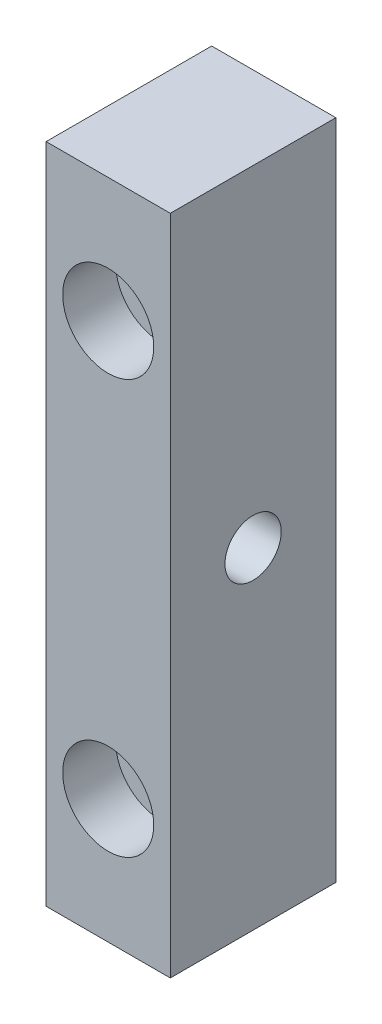
SolidWorks part; units mm, degrees
ref_plane "前视基准面" through (0, 0, 0) normal (0, 0, 1) x (1, 0, 0)
ref_plane "上视基准面" through (0, 0, 0) normal (0, 1, 0) x (1, 0, 0)
ref_plane "右视基准面" through (0, 0, 0) normal (1, 0, 0) x (0, 0, -1)
sketch "草图1" plane through (0, 0, 0) normal (0, 0, 1) x (1, 0, 0)
  line L1 (7.5, -40) -> (-7.5, -40)
  line L2 (7.5, -40) -> (7.5, 40)
  line L3 (7.5, 40) -> (-7.5, 40)
  line L4 (-7.5, -40) -> (-7.5, 40)
  line L5 (7.5, -40) -> (-7.5, 40) construction
  line L6 (7.5, 40) -> (-7.5, -40) construction
  point P0 (0, 0)
  dimension "D1" = 15
  dimension "D2" = 80
extrude "凸台-拉伸1" add sketch "草图1" along normal blind 20
sketch "草图2" plane through (7.5, 0, 0) normal (1, 0, 0) x (0, 0, -1)
  line L0 (-20, 0) -> (-10, 0) construction
  line L1 (-20, -40) -> (-20, 40) construction
  circle A0 centre (-10, 0) radius 4.5781
  dimension "D1" = 10
hole_wizard "M8 螺纹孔1" positions "3D草图1" profile "草图3" tap size "M8" standard "Iso"
sketch3d "3D草图1"
  point P0 (7.5, 0, 10)
sketch "草图3" plane through (7.5, 0, 10) normal (0, 1, 0) x (0, 0, -1)
  line L0 (0, 0) -> (0, 21.7929)
  line L1 (0, 21.7929) -> (3.4, 19.75)
  line L2 (3.4, 19.75) -> (3.4, 0)
  line L5 (3.4, 0) -> (0, 0)
  line L10 (0, 21.7929) -> (-3.4, 19.75) construction
  line L11 (0, -6.35) -> (0, 107.95) construction
  dimension "螺纹孔钻头直径" = 6.8
  dimension "螺纹孔钻头深度" = 19.75
  dimension "导头角度" = 118
sketch "草图4" plane through (0, 0, 20) normal (0, 0, 1) x (1, 0, 0)
  line L0 (0, 25) -> (0, 0) construction
  line L1 (0, 0) -> (-18.5111, 0) construction
  circle A0 centre (0, 25) radius 2.5
  circle A1 centre (0, -25) radius 2.5
  dimension "D1" = 50
hole_wizard "M6 六角凹头螺钉的柱形沉头孔1" positions "3D草图2" profile "草图5" counterbore size "M6" standard "Iso" end condition through all
sketch3d "3D草图2"
  point P0 (0, 25, 20)
  point P3 (0, -25, 20)
sketch "草图5" plane through (0, 25, 20) normal (1, 0, 0) x (0, -1, 0)
  line L0 (0, 0) -> (0, 20)
  line L1 (0, 20) -> (3.2, 20)
  line L3 (3.2, 20) -> (3.2, 6.4)
  line L4 (3.2, 6.4) -> (5.5, 6.4)
  line L5 (5.5, 6.4) -> (5.5, 0)
  line L7 (5.5, 0) -> (0, 0)
  line L11 (0, -6.35) -> (0, 107.95) construction
  dimension "通孔孔直径" = 6.4
  dimension "通孔孔深度" = 20
  dimension "柱形沉头孔直径" = 11
  dimension "柱形沉头孔深度" = 6.4
